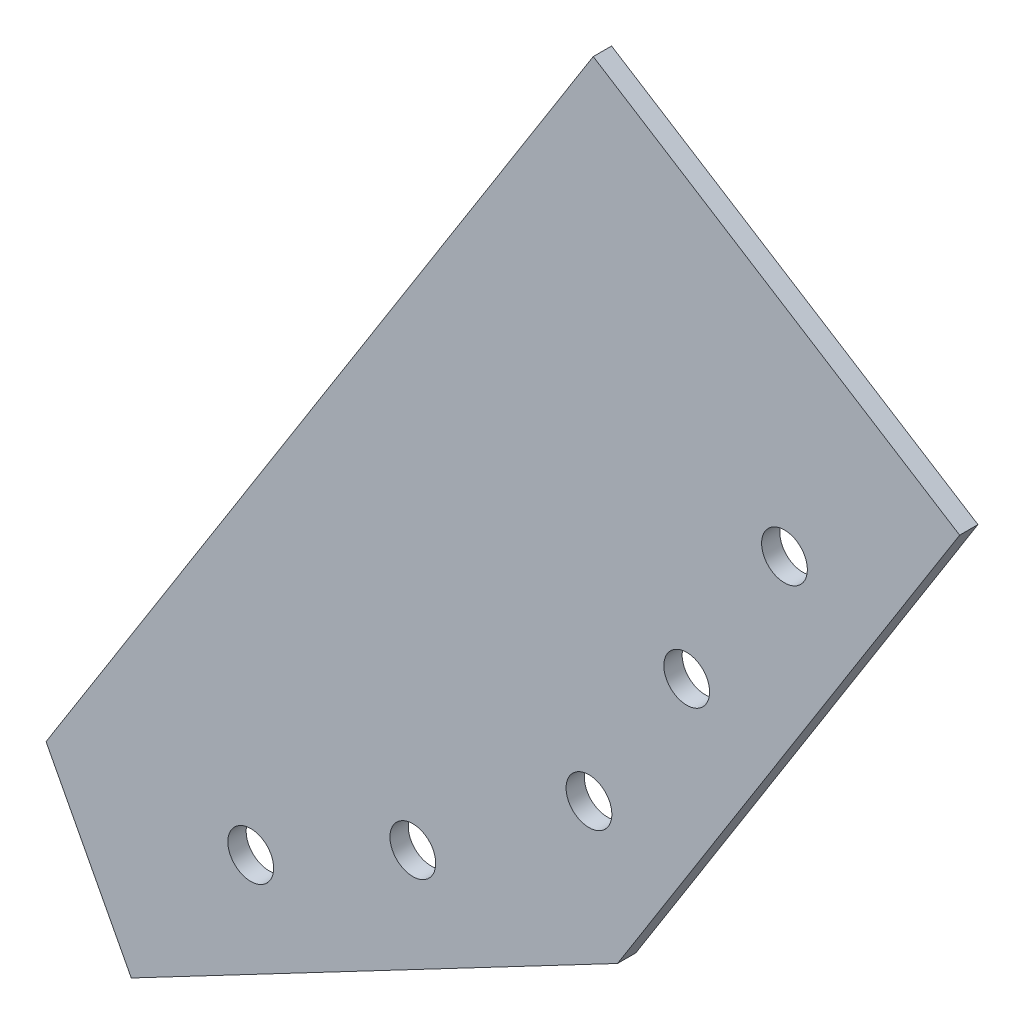
SolidWorks part; units mm, degrees
ref_plane "Front Plane" through (0, 0, 0) normal (0, 0, 1) x (1, 0, 0)
ref_plane "Top Plane" through (0, 0, 0) normal (0, 1, 0) x (1, 0, 0)
ref_plane "Right Plane" through (0, 0, 0) normal (1, 0, 0) x (0, 0, -1)
sketch "Sketch2" plane through (0, 0, 0) normal (0, 0, 1) x (1, 0, 0)
  line L0 (47.8064, 40.7768) -> (7.7911, 66.0357)
  line L1 (-51.9719, -28.6415) -> (7.7911, 66.0357)
  line L2 (47.8064, 40.7768) -> (10.4417, -18.4167)
  line L3 (10.4417, -18.4167) -> (-42.6631, -46.3431)
  line L4 (-42.6631, -46.3431) -> (-51.9719, -28.6415)
  dimension "D3" = 70
  dimension "D4" = 60
  dimension "D5" = 150
  dimension "D6" = 20
extrude "Boss-Extrude1" add sketch "Sketch2" along normal blind 2
ref_plane "Plane1" through (47.8064, 40.7768, 2) normal (0.5338, 0.8456, 0) x (0.8456, -0.5338, 0)
sketch "Sketch4" plane through (0, 0, 2) normal (0, 0, 1) x (1, 0, 0)
  line L0 (10.4417, -18.4167) -> (-7.2599, -27.7255)
  line L1 (-42.6631, -46.3431) -> (10.4417, -18.4167) construction
  line L2 (-7.2599, -27.7255) -> (-11.9143, -18.8747)
  dimension "D1" = 20
  dimension "D2" = 10
sketch "Sketch5" plane through (0, 0, 2) normal (0, 0, 1) x (1, 0, 0)
  circle A0 centre (-11.9143, -18.8747) radius 2.5
extrude "Cut-Extrude1" cut sketch "Sketch5" against normal blind 2
sketch "Sketch6" plane through (0, 0, 2) normal (0, 0, 1) x (1, 0, 0)
  line L0 (-42.6631, -46.3431) -> (-24.9615, -37.0343)
  line L1 (-42.6631, -46.3431) -> (10.4417, -18.4167) construction
  line L2 (-24.9615, -37.0343) -> (-29.6159, -28.1835)
  circle A0 centre (-29.6159, -28.1835) radius 2.5
  dimension "D1" = 20
  dimension "D2" = 10
  dimension "D3" = 90
extrude "Cut-Extrude2" cut sketch "Sketch6" against normal blind 2 contours A0
sketch "Sketch7" plane through (0, 0, 2) normal (0, 0, 1) x (1, 0, 0)
  line L0 (10.4417, -18.4167) -> (15.7795, -9.9605)
  line L1 (10.4417, -18.4167) -> (47.8064, 40.7768) construction
  line L2 (15.7795, -9.9605) -> (7.3233, -4.6227)
  circle A0 centre (7.3233, -4.6227) radius 2.5
  dimension "D1" = 10
  dimension "D2" = 10
extrude "Cut-Extrude3" cut sketch "Sketch7" against normal blind 2 contours A0
sketch "Sketch8" plane through (0, 0, 2) normal (0, 0, 1) x (1, 0, 0)
  line L0 (10.4417, -18.4167) -> (26.4552, 6.9519)
  line L1 (10.4417, -18.4167) -> (47.8064, 40.7768) construction
  line L2 (26.4552, 6.9519) -> (17.9989, 12.2898)
  circle A0 centre (17.9989, 12.2898) radius 2.5
  dimension "D1" = 30
  dimension "D2" = 10
extrude "Cut-Extrude4" cut sketch "Sketch8" against normal blind 40 contours A0
sketch "Sketch9" plane through (0, 0, 2) normal (0, 0, 1) x (1, 0, 0)
  line L0 (10.4417, -18.4167) -> (37.1308, 23.8644)
  line L1 (10.4417, -18.4167) -> (47.8064, 40.7768) construction
  line L2 (37.1308, 23.8644) -> (28.6746, 29.2022)
  circle A0 centre (28.6746, 29.2022) radius 2.5
  dimension "D1" = 50
  dimension "D2" = 10
extrude "Cut-Extrude5" cut sketch "Sketch9" against normal blind 40 contours A0
